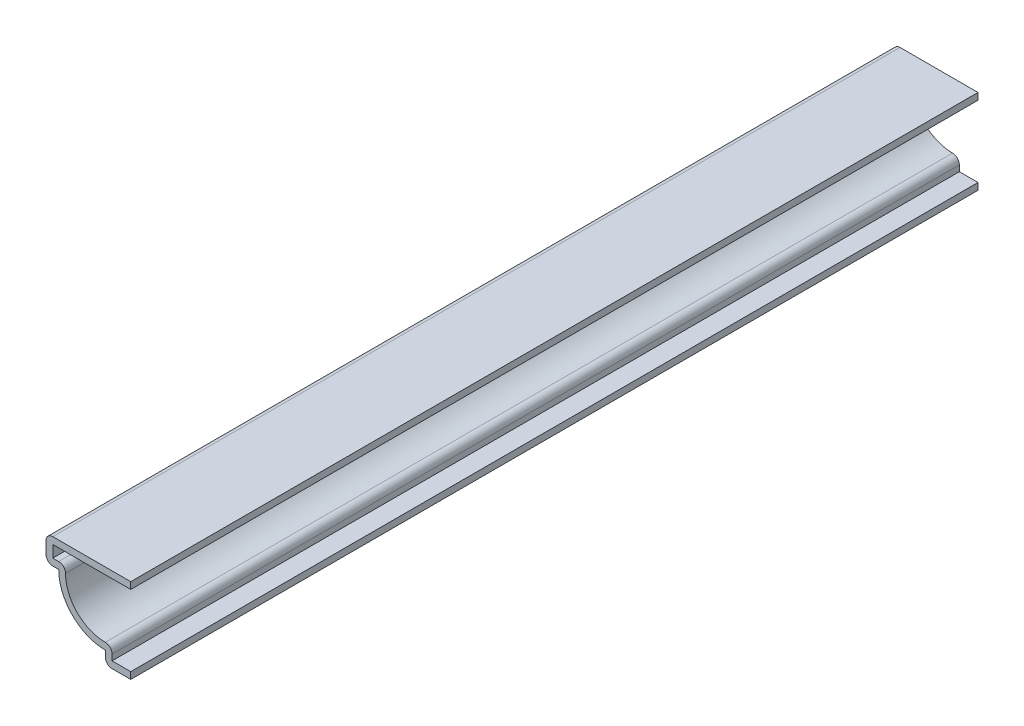
SolidWorks part; units mm, degrees
ref_plane "Front Plane" through (0, 0, 0) normal (0, 0, 1) x (1, 0, 0)
ref_plane "Top Plane" through (0, 0, 0) normal (0, 1, 0) x (1, 0, 0)
ref_plane "Right Plane" through (0, 0, 0) normal (1, 0, 0) x (0, 0, -1)
sketch "Sketch1" plane through (0, 0, 0) normal (0, 0, 1) x (1, 0, 0)
  line L0 (0, 0) -> (-15.875, 0) construction
  line L1 (0, 0) -> (0, 15.875) construction
  line L2 (0, 0) -> (-4.7625, 0)
  line L3 (-4.7625, 0) -> (-4.7625, 2.3813)
  line L4 (-13.4938, 11.1125) -> (-15.875, 11.1125)
  line L5 (-15.875, 11.1125) -> (-15.875, 15.875)
  line L6 (-15.875, 15.875) -> (0, 15.875)
  arc A0 (-4.7625, 2.3813) -> (-13.4938, 11.1125) centre (-4.7625, 11.1125) cw
  dimension "D1" = 15.875
  dimension "D2" = 15.875
  dimension "D3" = 15.875
  dimension "D4" = 2.3813
  dimension "D5" = 8.7312
  dimension "D6" = 8.7312
  dimension "D7" = 4.7625
extrude "Extrude-Thin1" add sketch "Sketch1" against normal blind 158.75 thin
fillet "Fillet1" radius 1.27 5 edges at (-4.7625, 0, -79.375) (-3.4925, 3.7601, -79.375) (-12.1149, 12.3825, -79.375) (-15.875, 11.1125, -79.375) (-15.875, 15.875, -79.375)
